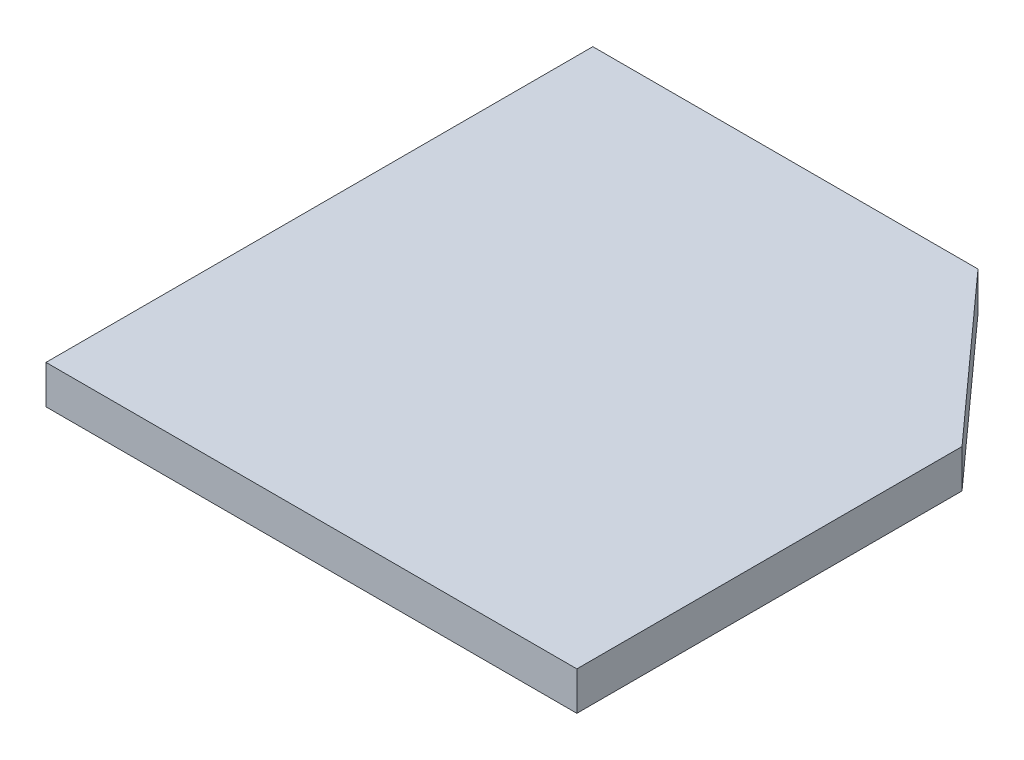
SolidWorks part; units mm, degrees
ref_plane "Спереди" through (0, 0, 0) normal (0, 0, 1) x (1, 0, 0)
ref_plane "Сверху" through (0, 0, 0) normal (0, 1, 0) x (1, 0, 0)
ref_plane "Справа" through (0, 0, 0) normal (1, 0, 0) x (0, 0, -1)
sketch "Эскиз1" plane through (0, 0, 0) normal (0, 1, 0) x (1, 0, 0)
  line L0 (0, 0) -> (68.9142, 0)
  line L1 (0, 0) -> (0, 70.9877)
  line L2 (68.9142, 0) -> (68.9142, 50)
  line L3 (0, 70.9877) -> (50, 70.9877)
  line L4 (50, 70.9877) -> (68.9142, 50)
extrude "Бобышка-Вытянуть1" add sketch "Эскиз1" along normal blind 5
